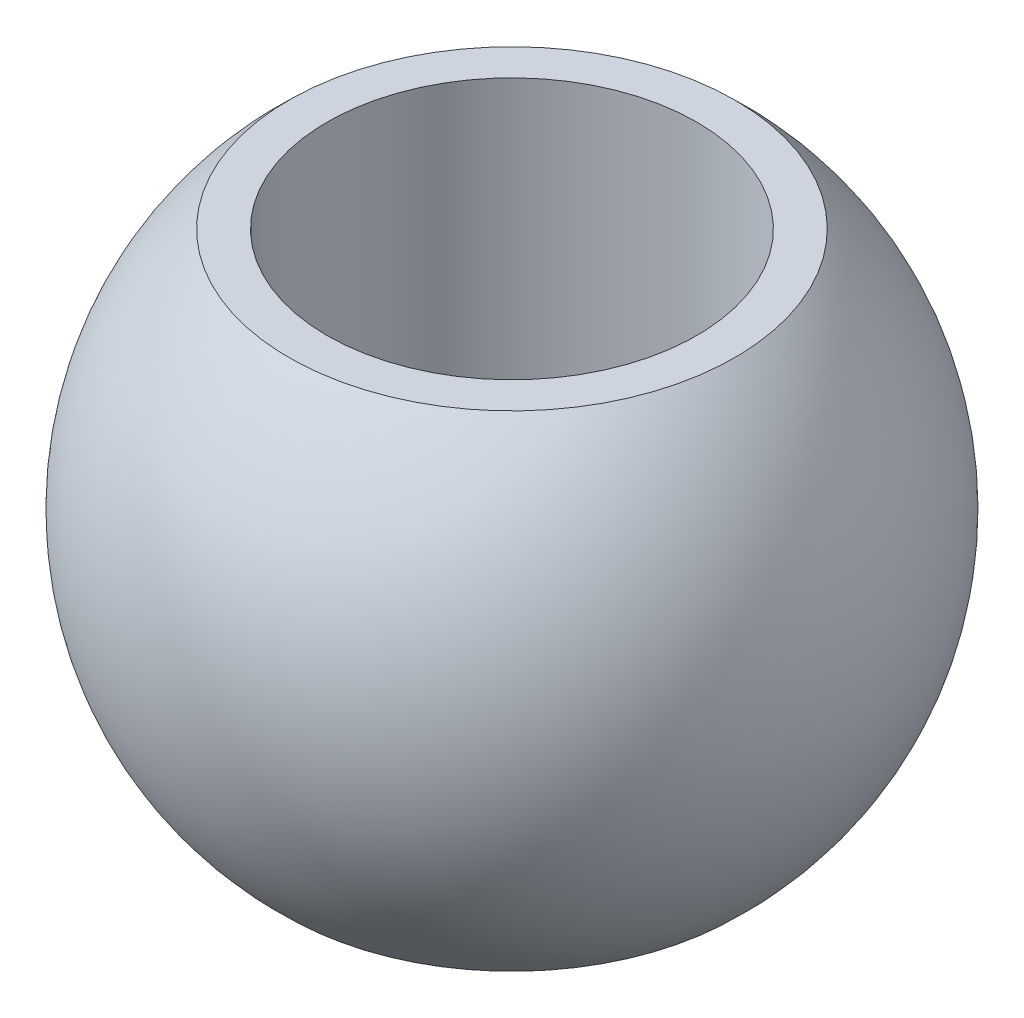
SolidWorks part; units mm, degrees
material "1.0545 (S355N)"
ref_plane "Płaszczyzna przednia" through (0, 0, 0) normal (0, 0, 1) x (1, 0, 0)
ref_plane "Płaszczyzna górna" through (0, 0, 0) normal (0, 1, 0) x (1, 0, 0)
ref_plane "Płaszczyzna prawa" through (0, 0, 0) normal (1, 0, 0) x (0, 0, -1)
sketch "Szkic1" plane through (0, 0, 0) normal (0, 0, 1) x (1, 0, 0)
  line L0 (0, -11.1) -> (0, 11.1) construction
  line L1 (8, -10.5) -> (8, 10.5)
  line L2 (8, 10.5) -> (9.6487, 10.5)
  line L3 (8, -10.5) -> (9.6487, -10.5)
  arc A0 (9.6487, -10.5) -> (9.6487, 10.5) centre (0, 0) ccw
  point P6 (8, 0)
  dimension "d3" = 28.52
  dimension "d1" = 8
  dimension "b1" = 21
revolve "Obrót1" add sketch "Szkic1" angle 360 about L0
